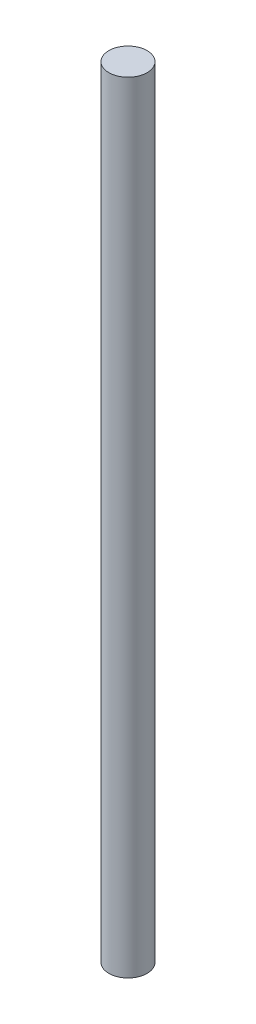
SolidWorks part; units mm, degrees
ref_plane "Front Plane" through (0, 0, 0) normal (0, 0, 1) x (1, 0, 0)
ref_plane "Top Plane" through (0, 0, 0) normal (0, 1, 0) x (1, 0, 0)
ref_plane "Right Plane" through (0, 0, 0) normal (1, 0, 0) x (0, 0, -1)
sketch "Sketch1" plane through (0, 0, 0) normal (0, 1, 0) x (1, 0, 0)
  circle A0 centre (0, 0) radius 2.5
  dimension "D1" = 5
extrude "Boss-Extrude1" add sketch "Sketch1" along normal blind 102
